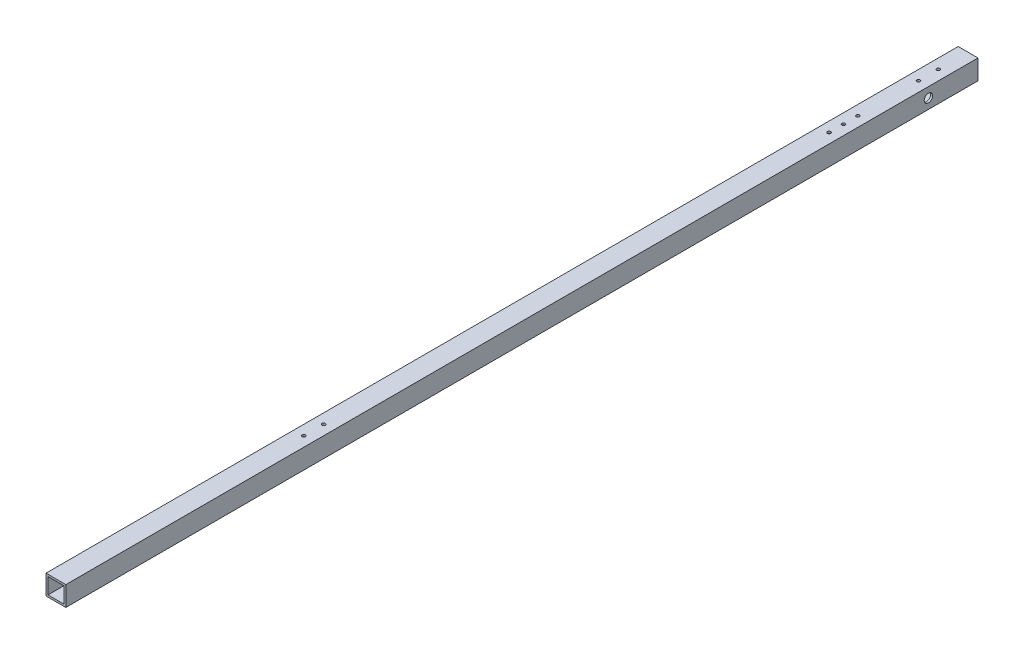
SolidWorks part; units mm, degrees
ref_plane "正面" through (0, 0, 0) normal (0, 0, 1) x (1, 0, 0)
ref_plane "平面" through (0, 0, 0) normal (0, 1, 0) x (1, 0, 0)
ref_plane "右側面" through (0, 0, 0) normal (1, 0, 0) x (0, 0, -1)
sketch "ｽｹｯﾁ1" plane through (0, 0, 0) normal (0, 0, 1) x (1, 0, 0)
  line L1 (-10, 10) -> (10, 10)
  line L2 (-10, 10) -> (-10, -10)
  line L3 (-10, -10) -> (10, -10)
  line L4 (10, 10) -> (10, -10)
  line L5 (-10, 10) -> (10, -10) construction
  line L6 (-10, -10) -> (10, 10) construction
  line L7 (-8, 8) -> (8, 8)
  line L8 (-8, 8) -> (-8, -8)
  line L9 (-8, -8) -> (8, -8)
  line L10 (8, 8) -> (8, -8)
  line L11 (-8, 8) -> (8, -8) construction
  line L12 (-8, -8) -> (8, 8) construction
  point P0 (0, 0)
  point P6 (0, 0)
  dimension "D1" = 20
  dimension "D2" = 20
  dimension "D3" = 16
  dimension "D4" = 16
extrude "ﾎﾞｽ - 押し出し1" add sketch "ｽｹｯﾁ1" along normal blind 970
sketch "ｽｹｯﾁ2" plane through (10, 0, 0) normal (1, 0, 0) x (0, 0, -1)
  line L0 (-970, 0) -> (-710, 0)
  line L1 (-970, -10) -> (-970, 10) construction
  line L2 (-710, 0) -> (-890.4665, 0)
  line L3 (-890.4665, 0) -> (-845.8821, 0)
  line L4 (-845.8821, 0) -> (-803.5394, 0)
  line L5 (-710, 0) -> (-670, 0)
  line L6 (-670, 0) -> (-50, 0)
  line L7 (-50, 0) -> (-40, 0)
  line L8 (-710, 0) -> (-730, 0)
  circle A0 centre (-710, 0) radius 1
  circle A4 centre (-670, 0) radius 2.2
  circle A5 centre (-50, 0) radius 4.25
  circle A6 centre (-40, 0) radius 1
  circle A7 centre (-730, 0) radius 1
  dimension "D5" = 2
  dimension "D6" = 8.5
  dimension "D7" = 4.4
  dimension "D8" = 2
  dimension "D10" = 2
  dimension "D1" = 260
  dimension "D2" = 40
  dimension "D3" = 620
  dimension "D4" = 10
  dimension "D9" = 20
extrude "ｶｯﾄ - 押し出し1" cut sketch "ｽｹｯﾁ2" against normal blind 20 contours L7 A5 L6
sketch "ｽｹｯﾁ3" plane through (0, 10, 0) normal (0, 1, 0) x (1, 0, 0)
  line L0 (0, -970) -> (0, -690)
  line L1 (10, -970) -> (-10, -970) construction
  line L2 (0, -690) -> (0, -670)
  line L3 (0, -670) -> (0, -20)
  line L4 (0, -670) -> (0, -650)
  circle A0 centre (0, -690) radius 2.2
  circle A1 centre (0, -670) radius 1
  circle A2 centre (0, -20) radius 2.2
  circle A3 centre (0, -650) radius 1
  dimension "D2" = 4.4
  dimension "D4" = 2
  dimension "D6" = 4.4
  dimension "D8" = 2
  dimension "D1" = 280
  dimension "D3" = 20
  dimension "D5" = 650
  dimension "D7" = 20
extrude "ｶｯﾄ - 押し出し2" cut sketch "ｽｹｯﾁ3" against normal blind 10 contours L3 A3 | L3 A3 | L2 A1 L3 | L3 A1 L2
sketch "ｽｹｯﾁ5" plane through (0, 10, 0) normal (0, 1, 0) x (1, 0, 0)
  line L0 (0, 0) -> (0, -111.21)
  line L1 (0, -111.21) -> (0, -140.21)
  circle A0 centre (0, -111.21) radius 2.2
  circle A1 centre (0, -140.21) radius 2.2
  dimension "D2" = 4.4
  dimension "D4" = 4.4
  dimension "D1" = 111.21
  dimension "D3" = 29
sketch "ｽｹｯﾁ6" plane through (0, 0, 970) normal (0, 0, 1) x (1, 0, 0)
  line L1 (13.9129, -10.9209) -> (-13.9129, -10.9209)
  line L2 (13.9129, -10.9209) -> (13.9129, 10.9209)
  line L3 (13.9129, 10.9209) -> (-13.9129, 10.9209)
  line L4 (-13.9129, -10.9209) -> (-13.9129, 10.9209)
  line L5 (13.9129, -10.9209) -> (-13.9129, 10.9209) construction
  line L6 (13.9129, 10.9209) -> (-13.9129, -10.9209) construction
  point P0 (0, 0)
extrude "ｶｯﾄ - 押し出し8" cut sketch "ｽｹｯﾁ6" against normal blind 50
sketch "ｽｹｯﾁ8" plane through (-10, 0, 0) normal (-1, 0, 0) x (0, 0, 1)
  line L0 (0, 0) -> (99, 0)
  line L1 (99, 0) -> (148, 0)
  circle A0 centre (99, 0) radius 2.2
  circle A1 centre (148, 0) radius 2.2
  dimension "D2" = 4.4
  dimension "D4" = 4.4
  dimension "D1" = 99
  dimension "D3" = 49
sketch "ｽｹｯﾁ9" plane through (0, 10, 0) normal (0, 1, 0) x (1, 0, 0)
  line L0 (0, 0) -> (0, -10)
  line L1 (0, -10) -> (0, -30)
  line L2 (0, -30) -> (0, -50)
  circle A0 centre (0, -30) radius 1
  circle A1 centre (0, -50) radius 1
  dimension "D4" = 2
  dimension "D5" = 2
  dimension "D1" = 10
  dimension "D2" = 20
  dimension "D3" = 20
extrude "ｶｯﾄ - 押し出し9" cut sketch "ｽｹｯﾁ9" against normal blind 10
sketch "ｽｹｯﾁ10" plane through (0, 10, 0) normal (0, 1, 0) x (1, 0, 0)
  line L0 (0, -111.21) -> (0, -125.71)
  circle A0 centre (0, -125.71) radius 2.1
  dimension "D2" = 4.2
  dimension "D1" = 14.5
hole_wizard "M4x0.7 ねじ穴3" positions "3Dｽｹｯﾁ4" profile "ｽｹｯﾁ15" tap size "M4x0.7" standard "JIS" end condition through all
sketch3d "3Dｽｹｯﾁ4"
  point P0 (0, 10, 111.21)
  point P3 (0, 10, 140.21)
sketch "ｽｹｯﾁ15" plane through (0, 10, 111.21) normal (1, 0, 0) x (0, 0, 1)
  line L0 (0, 0) -> (0, 20)
  line L1 (0, 20) -> (1.65, 20)
  line L2 (1.65, 20) -> (1.65, 0)
  line L5 (1.65, 0) -> (0, 0)
  line L11 (0, -6.35) -> (0, 107.95) construction
  dimension "次ｻｰﾌｪｽまでのねじ下穴ﾄﾞﾘﾙ直径" = 3.3
  dimension "次ｻｰﾌｪｽまでのねじ下穴ﾄﾞﾘﾙの深さ" = 20
cosmetic thread "穴のねじ山4" parameters "D2"=4
cosmetic thread "穴のねじ山5" parameters "D2"=4
hole_wizard "M4x0.7 ねじ穴2" positions "3Dｽｹｯﾁ3" profile "ｽｹｯﾁ14" tap size "M4x0.7" standard "JIS" end condition through all
sketch3d "3Dｽｹｯﾁ3"
  point P0 (0, 10, 125.71)
sketch "ｽｹｯﾁ14" plane through (0, 10, 125.71) normal (1, 0, 0) x (0, 0, 1)
  line L0 (0, 0) -> (0, 20)
  line L1 (0, 20) -> (1.65, 20)
  line L2 (1.65, 20) -> (1.65, 0)
  line L5 (1.65, 0) -> (0, 0)
  line L11 (0, -6.35) -> (0, 107.95) construction
  dimension "次ｻｰﾌｪｽまでのねじ下穴ﾄﾞﾘﾙ直径" = 3.3
  dimension "次ｻｰﾌｪｽまでのねじ下穴ﾄﾞﾘﾙの深さ" = 20
cosmetic thread "穴のねじ山3" parameters "D2"=4
hole_wizard "M4x0.7 ねじ穴7" positions "3Dｽｹｯﾁ10" profile "ｽｹｯﾁ22" tap size "M4x0.7" standard "JIS"
sketch3d "3Dｽｹｯﾁ10"
  line L0 (0, 8, 650) -> (0, 10, 650) construction
  line L1 (0, 8, 670) -> (0, 10, 670) construction
  point P0 (0, 10, 650)
  point P4 (0, 10, 670)
sketch "ｽｹｯﾁ22" plane through (0, 10, 650) normal (1, 0, 0) x (0, 0, 1)
  line L0 (0, 0) -> (0, 12.4914)
  line L1 (0, 12.4914) -> (1.65, 11.5)
  line L2 (1.65, 11.5) -> (1.65, 0)
  line L5 (1.65, 0) -> (0, 0)
  line L10 (0, 12.4914) -> (-1.65, 11.5) construction
  line L11 (0, -6.35) -> (0, 107.95) construction
  dimension "ねじ下穴ﾄﾞﾘﾙ直径" = 3.3
  dimension "ねじ下穴ﾄﾞﾘﾙの深さ" = 11.5
  dimension "ﾄﾞﾘﾙ角度" = 118
cosmetic thread "穴のねじ山12" parameters "D1"=2, "D2"=4
cosmetic thread "穴のねじ山13" parameters "D1"=2, "D2"=4
hole_wizard "M4x0.7 ねじ穴9" positions "3Dｽｹｯﾁ13" profile "ｽｹｯﾁ25" tap size "M4x0.7" standard "JIS"
sketch3d "3Dｽｹｯﾁ13"
  line L0 (0, 8, 30) -> (0, 10, 30) construction
  line L1 (0, 8, 50) -> (0, 10, 50) construction
  point P0 (0, 10, 30)
  point P4 (0, 10, 50)
sketch "ｽｹｯﾁ25" plane through (0, 10, 30) normal (1, 0, 0) x (0, 0, 1)
  line L0 (0, 0) -> (0, 12.4914)
  line L1 (0, 12.4914) -> (1.65, 11.5)
  line L2 (1.65, 11.5) -> (1.65, 0)
  line L5 (1.65, 0) -> (0, 0)
  line L10 (0, 12.4914) -> (-1.65, 11.5) construction
  line L11 (0, -6.35) -> (0, 107.95) construction
  dimension "ねじ下穴ﾄﾞﾘﾙ直径" = 3.3
  dimension "ねじ下穴ﾄﾞﾘﾙの深さ" = 11.5
  dimension "ﾄﾞﾘﾙ角度" = 118
cosmetic thread "穴のねじ山14" parameters "D1"=2, "D2"=4
cosmetic thread "穴のねじ山15" parameters "D1"=2, "D2"=4
sketch "ｽｹｯﾁ26" plane through (-10, 0, 0) normal (-1, 0, 0) x (0, 0, 1)
  line L0 (0, 0) -> (40, 0)
  line L1 (0, 10) -> (0, -10) construction
  line L2 (920, 0) -> (730, 0)
  line L3 (920, 10) -> (920, -10) construction
  line L4 (730, 0) -> (710, 0)
  circle A0 centre (40, 0) radius 1
  circle A1 centre (710, 0) radius 1
  circle A2 centre (730, 0) radius 1
  dimension "D2" = 2
  dimension "D5" = 2
  dimension "D6" = 2
  dimension "D1" = 40
  dimension "D3" = 190
  dimension "D4" = 20
extrude "ｶｯﾄ - 押し出し10" cut sketch "ｽｹｯﾁ26" against normal blind 10
hole_wizard "M4x0.7 ねじ穴10" positions "3Dｽｹｯﾁ14" profile "ｽｹｯﾁ27" tap size "M4x0.7" standard "JIS"
sketch3d "3Dｽｹｯﾁ14"
  line L0 (-8, 0, 730) -> (-10, 0, 730) construction
  line L1 (-8, 0, 710) -> (-10, 0, 710) construction
  line L2 (-8, 0, 40) -> (-10, 0, 40) construction
  point P0 (-10, 0, 730)
  point P4 (-10, 0, 710)
  point P8 (-10, 0, 40)
sketch "ｽｹｯﾁ27" plane through (-10, 0, 730) normal (0, 1, 0) x (0, 0, 1)
  line L0 (0, 0) -> (0, 12.4914)
  line L1 (0, 12.4914) -> (1.65, 11.5)
  line L2 (1.65, 11.5) -> (1.65, 0)
  line L5 (1.65, 0) -> (0, 0)
  line L10 (0, 12.4914) -> (-1.65, 11.5) construction
  line L11 (0, -6.35) -> (0, 107.95) construction
  dimension "ねじ下穴ﾄﾞﾘﾙ直径" = 3.3
  dimension "ねじ下穴ﾄﾞﾘﾙの深さ" = 11.5
  dimension "ﾄﾞﾘﾙ角度" = 118
cosmetic thread "穴のねじ山17" parameters "D1"=2, "D2"=4
cosmetic thread "穴のねじ山18" parameters "D1"=2, "D2"=4
cosmetic thread "穴のねじ山19" parameters "D1"=2, "D2"=4
